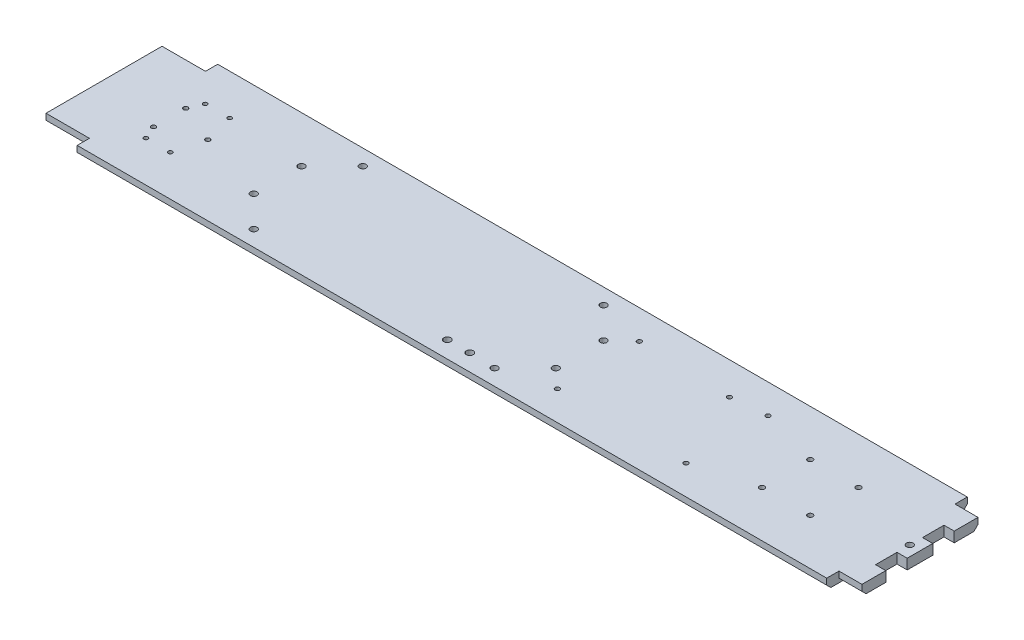
SolidWorks part; units mm, degrees
ref_plane "Front Plane" through (0, 0, 0) normal (0, 0, 1) x (1, 0, 0)
ref_plane "Top Plane" through (0, 0, 0) normal (0, 1, 0) x (1, 0, 0)
ref_plane "Right Plane" through (0, 0, 0) normal (1, 0, 0) x (0, 0, -1)
sketch "Sketch1" plane through (0, 0, 0) normal (0, 1, 0) x (1, 0, 0)
  line L1 (-260, 43.688) -> (260, 43.688)
  line L2 (-260, 43.688) -> (-260, -43.688)
  line L3 (-260, -43.688) -> (260, -43.688)
  line L4 (260, 43.688) -> (260, -43.688)
  point P4 (0, -43.688)
  point P6 (-260, 0)
  dimension "D1" = 520
  dimension "D2" = 87.376
extrude "Boss-Extrude1" add sketch "Sketch1" along normal blind 6.35
sketch "Sketch3" plane through (0, 6.35, 0) normal (0, 1, 0) x (1, 0, 0)
  line L1 (-260, 43.688) -> (-233, 43.688)
  line L2 (-260, 43.688) -> (-260, 36.068)
  line L3 (-260, 36.068) -> (-233, 36.068)
  line L4 (-233, 43.688) -> (-233, 36.068)
  line L5 (-260, -43.688) -> (-233, -43.688)
  line L6 (-260, -43.688) -> (-260, -36.068)
  line L7 (-260, -36.068) -> (-233, -36.068)
  line L8 (-233, -43.688) -> (-233, -36.068)
  line L9 (260, -43.688) -> (233, -43.688)
  line L10 (260, -43.688) -> (260, -36.068)
  line L11 (260, -36.068) -> (233, -36.068)
  line L12 (233, -43.688) -> (233, -36.068)
  line L13 (260, 43.688) -> (233, 43.688)
  line L14 (260, 43.688) -> (260, 36.068)
  line L15 (260, 36.068) -> (233, 36.068)
  line L16 (233, 43.688) -> (233, 36.068)
  dimension "D1" = 27
  dimension "D2" = 7.62
extrude "Cut-Extrude2" cut sketch "Sketch3" against normal through all
sketch "Sketch6" plane through (0, 6.35, 0) normal (0, 1, 0) x (1, 0, 0)
  line L0 (260, -36.068) -> (233, -36.068) construction
  line L1 (260, 36.068) -> (247.3, 36.068)
  line L2 (260, 36.068) -> (260, -36.068)
  line L3 (260, -36.068) -> (247.3, -36.068)
  line L4 (247.3, 36.068) -> (247.3, -36.068)
  dimension "D1" = 12.7
extrude "Cut-Extrude5" cut sketch "Sketch6" against normal through all
sketch "Sketch8" plane through (0, 6.35, 0) normal (0, 1, 0) x (1, 0, 0)
  line L0 (-219.2, 10) -> (-219.2, -10) construction
  line L1 (-195.5, 0) -> (-219.2, 0) construction
  line L2 (-260, 36.068) -> (-260, -36.068) construction
  circle A0 centre (-219.2, 10) radius 1.4
  circle A1 centre (-219.2, -10) radius 1.4
  circle A2 centre (-195.5, 0) radius 1.4
  point P6 (-219.2, 0)
  point P10 (-260, 0)
  dimension "D4" = 2.8
  dimension "D1" = 20
  dimension "D2" = 23.7
  dimension "D3" = 40.8
extrude "Cut-Extrude7" cut sketch "Sketch8" against normal through all
sketch "Sketch9" plane through (0, 6.35, 0) normal (0, 1, 0) x (1, 0, 0)
  line L0 (-152.05, 14.84) -> (-152.05, -14.84) construction
  line L1 (-133, 33.89) -> (-133, -33.89) construction
  line L2 (-260, 36.068) -> (-260, -36.068) construction
  circle A0 centre (-133, 33.89) radius 2.05
  circle A1 centre (-152.05, 14.84) radius 2.05
  circle A2 centre (-152.05, -14.84) radius 2.05
  circle A3 centre (-133, -33.89) radius 2.05
  circle A4 centre (16.68, 33.89) radius 2.05
  circle A5 centre (35.73, 14.84) radius 2.05
  circle A6 centre (35.73, -14.84) radius 2.05
  circle A7 centre (16.68, -33.89) radius 2.05
  point P16 (-133, 0)
  point P17 (-152.05, 0)
  point P20 (-260, 0)
  dimension "D1" = 4.1
  dimension "D2" = 29.68
  dimension "D3" = 67.78
  dimension "D4" = 19.05
  dimension "D5" = 19.05
  dimension "D6" = 149.68
  dimension "D7" = 107.95
extrude "Cut-Extrude8" cut sketch "Sketch9" against normal through all
chamfer "Chamfer1" distance 2.54 angle 45 6 edges at (240.15, 0, 36.068) (240.15, 0, -36.068) (0, 0, -43.688) (0, 0, 43.688) (-246.5, 0, 36.068) (-246.5, 0, -36.068)
sketch "Sketch10" plane through (0, 6.35, 0) normal (0, 1, 0) x (1, 0, 0)
  line L0 (47.34, 25.5) -> (47.34, -25.5) construction
  line L1 (-260, 36.068) -> (-260, -36.068) construction
  circle A0 centre (47.34, 25.5) radius 1.4
  circle A1 centre (127.34, 25.5) radius 1.4
  circle A2 centre (47.34, -25.5) radius 1.4
  circle A3 centre (127.34, -25.5) radius 1.4
  circle A4 centre (105.34, 23.5) radius 1.4
  point P10 (47.34, 0)
  point P11 (-260, 0)
  dimension "D4" = 2.8
  dimension "D1" = 307.34
  dimension "D2" = 80
  dimension "D3" = 51
  dimension "D5" = 49
  dimension "D6" = 58
extrude "Cut-Extrude9" cut sketch "Sketch10" against normal through all
sketch "Sketch11" plane through (0, 6.35, 0) normal (0, 1, 0) x (1, 0, 0)
  line L0 (247.3, 36.068) -> (247.3, -36.068) construction
  circle A0 centre (240.95, 0) radius 2.05
  point P4 (247.3, 0)
  dimension "D1" = 4.1
  dimension "D2" = 6.35
extrude "Cut-Extrude10" cut sketch "Sketch11" against normal through all
sketch "Sketch12" plane through (0, 6.35, 0) normal (0, 1, 0) x (1, 0, 0)
  line L0 (-215.55, 18.415) -> (-215.55, -18.415) construction
  line L1 (-260, 36.068) -> (-260, -36.068) construction
  circle A0 centre (-215.55, -18.415) radius 1.27
  circle A1 centre (-215.55, 18.415) radius 1.27
  circle A2 centre (-200.31, 18.415) radius 1.27
  circle A3 centre (-200.31, -18.415) radius 1.27
  point P10 (-215.55, 0)
  point P11 (-260, 0)
  dimension "D4" = 2.54
  dimension "D1" = 44.45
  dimension "D2" = 36.83
  dimension "D3" = 15.24
extrude "Cut-Extrude11" cut sketch "Sketch12" against normal through all
sketch "Sketch13" plane through (0, 6.35, 0) normal (0, 1, 0) x (1, 0, 0)
  line L0 (247.3, 36.068) -> (247.3, -36.068) construction
  line L1 (247.3, -7.9375) -> (240.95, -7.9375)
  line L2 (247.3, -7.9375) -> (247.3, -21.2725)
  line L3 (247.3, -21.2725) -> (240.95, -21.2725)
  line L4 (240.95, -7.9375) -> (240.95, -21.2725)
  line L5 (247.3, -7.9375) -> (247.3, 7.9375) construction
  line L6 (247.3, 7.9375) -> (240.95, 7.9375)
  line L7 (247.3, 7.9375) -> (247.3, 21.2725)
  line L8 (247.3, 21.2725) -> (240.95, 21.2725)
  line L9 (240.95, 7.9375) -> (240.95, 21.2725)
  point P10 (240.95, -14.605)
  point P11 (240.95, 14.605)
  point P12 (247.3, 0)
  point P13 (247.3, 0)
  dimension "D1" = 29.21
  dimension "D2" = 6.35
  dimension "D3" = 13.335
extrude "Cut-Extrude12" cut sketch "Sketch13" against normal through all
sketch "Sketch14" plane through (0, 6.35, 0) normal (0, 1, 0) x (1, 0, 0)
  line L0 (-260, 36.068) -> (-260, -36.068) construction
  line L1 (-233, -43.688) -> (233, -43.688) construction
  circle A0 centre (164.053, -15) radius 1.6
  circle A1 centre (194.053, -15) radius 1.6
  circle A2 centre (164.053, 15) radius 1.6
  circle A3 centre (194.053, 15) radius 1.6
  dimension "D5" = 3.2
  dimension "D1" = 424.053
  dimension "D2" = 28.688
  dimension "D3" = 30
  dimension "D4" = 30
extrude "Cut-Extrude13" cut sketch "Sketch14" against normal through all
sketch "Sketch15" plane through (0, 6.35, 0) normal (0, 1, 0) x (1, 0, 0)
  line L0 (-233, -43.688) -> (233, -43.688) construction
  circle A0 centre (0.68, -33.274) radius 2.15
  circle A2 centre (16.68, -33.89) radius 2.05 construction
  circle A3 centre (-13.32, -33.274) radius 2.15
  dimension "D4" = 4.3
  dimension "D1" = 10.414
  dimension "D2" = 16
  dimension "D3" = 14
extrude "Cut-Extrude14" cut sketch "Sketch15" against normal through all
